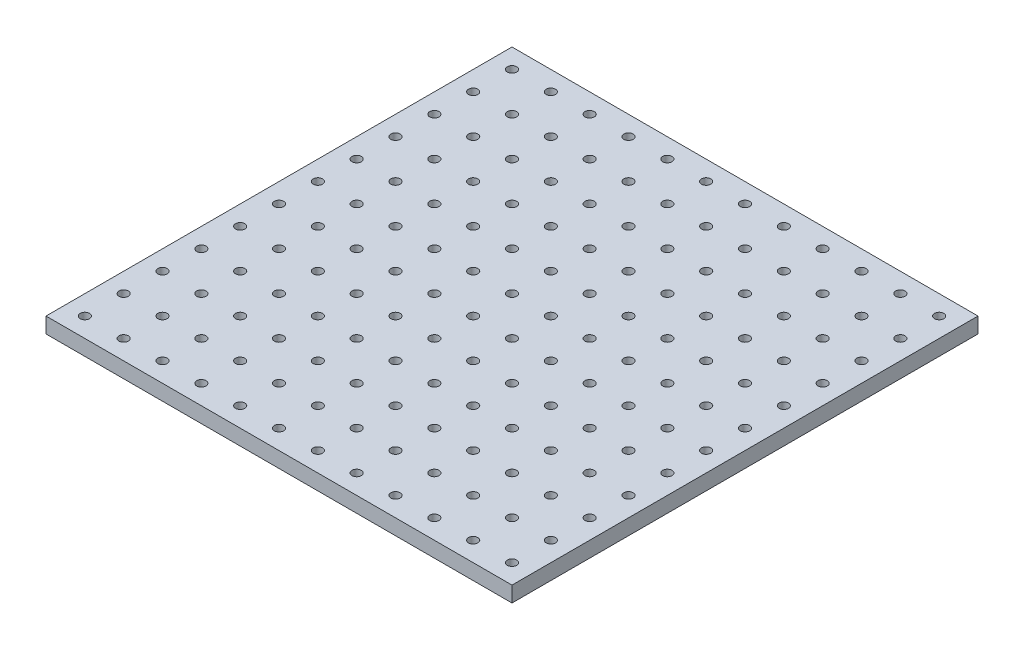
SolidWorks part; units mm, degrees
ref_plane "정면" through (0, 0, 0) normal (0, 0, 1) x (1, 0, 0)
ref_plane "윗면" through (0, 0, 0) normal (0, 1, 0) x (1, 0, 0)
ref_plane "우측면" through (0, 0, 0) normal (1, 0, 0) x (0, 0, -1)
sketch "스케치2" plane through (0, 0, 0) normal (0, 1, 0) x (1, 0, 0)
  line L1 (-150, 150) -> (150, 150)
  line L2 (-150, 150) -> (-150, -150)
  line L3 (-150, -150) -> (150, -150)
  line L4 (150, 150) -> (150, -150)
  circle A0 centre (-137.5, -137.5) radius 3
  circle A1 centre (-112.5, -137.5) radius 3
  circle A2 centre (-87.5, -137.5) radius 3
  circle A3 centre (-62.5, -137.5) radius 3
  circle A4 centre (-37.5, -137.5) radius 3
  circle A5 centre (-12.5, -137.5) radius 3
  circle A6 centre (12.5, -137.5) radius 3
  circle A7 centre (37.5, -137.5) radius 3
  circle A8 centre (62.5, -137.5) radius 3
  circle A9 centre (87.5, -137.5) radius 3
  circle A10 centre (112.5, -137.5) radius 3
  circle A11 centre (137.5, -137.5) radius 3
  circle A12 centre (-112.5, -112.5) radius 3
  circle A13 centre (-87.5, -112.5) radius 3
  circle A14 centre (-62.5, -112.5) radius 3
  circle A15 centre (-37.5, -112.5) radius 3
  circle A16 centre (-12.5, -112.5) radius 3
  circle A17 centre (12.5, -112.5) radius 3
  circle A18 centre (37.5, -112.5) radius 3
  circle A19 centre (62.5, -112.5) radius 3
  circle A20 centre (87.5, -112.5) radius 3
  circle A21 centre (112.5, -112.5) radius 3
  circle A22 centre (137.5, -112.5) radius 3
  circle A23 centre (-112.5, -87.5) radius 3
  circle A24 centre (-87.5, -87.5) radius 3
  circle A25 centre (-62.5, -87.5) radius 3
  circle A26 centre (-37.5, -87.5) radius 3
  circle A27 centre (-12.5, -87.5) radius 3
  circle A28 centre (12.5, -87.5) radius 3
  circle A29 centre (37.5, -87.5) radius 3
  circle A30 centre (62.5, -87.5) radius 3
  circle A31 centre (87.5, -87.5) radius 3
  circle A32 centre (112.5, -87.5) radius 3
  circle A33 centre (137.5, -87.5) radius 3
  circle A34 centre (-112.5, -62.5) radius 3
  circle A35 centre (-87.5, -62.5) radius 3
  circle A36 centre (-62.5, -62.5) radius 3
  circle A37 centre (-37.5, -62.5) radius 3
  circle A38 centre (-12.5, -62.5) radius 3
  circle A39 centre (12.5, -62.5) radius 3
  circle A40 centre (37.5, -62.5) radius 3
  circle A41 centre (62.5, -62.5) radius 3
  circle A42 centre (87.5, -62.5) radius 3
  circle A43 centre (112.5, -62.5) radius 3
  circle A44 centre (137.5, -62.5) radius 3
  circle A45 centre (-112.5, -37.5) radius 3
  circle A46 centre (-87.5, -37.5) radius 3
  circle A47 centre (-62.5, -37.5) radius 3
  circle A48 centre (-37.5, -37.5) radius 3
  circle A49 centre (-12.5, -37.5) radius 3
  circle A50 centre (12.5, -37.5) radius 3
  circle A51 centre (37.5, -37.5) radius 3
  circle A52 centre (62.5, -37.5) radius 3
  circle A53 centre (87.5, -37.5) radius 3
  circle A54 centre (112.5, -37.5) radius 3
  circle A55 centre (137.5, -37.5) radius 3
  circle A56 centre (-112.5, -12.5) radius 3
  circle A57 centre (-87.5, -12.5) radius 3
  circle A58 centre (-62.5, -12.5) radius 3
  circle A59 centre (-37.5, -12.5) radius 3
  circle A60 centre (-12.5, -12.5) radius 3
  circle A61 centre (12.5, -12.5) radius 3
  circle A62 centre (37.5, -12.5) radius 3
  circle A63 centre (62.5, -12.5) radius 3
  circle A64 centre (87.5, -12.5) radius 3
  circle A65 centre (112.5, -12.5) radius 3
  circle A66 centre (137.5, -12.5) radius 3
  circle A67 centre (-112.5, 12.5) radius 3
  circle A68 centre (-87.5, 12.5) radius 3
  circle A69 centre (-62.5, 12.5) radius 3
  circle A70 centre (-37.5, 12.5) radius 3
  circle A71 centre (-12.5, 12.5) radius 3
  circle A72 centre (12.5, 12.5) radius 3
  circle A73 centre (37.5, 12.5) radius 3
  circle A74 centre (62.5, 12.5) radius 3
  circle A75 centre (87.5, 12.5) radius 3
  circle A76 centre (112.5, 12.5) radius 3
  circle A77 centre (137.5, 12.5) radius 3
  circle A78 centre (-112.5, 37.5) radius 3
  circle A79 centre (-87.5, 37.5) radius 3
  circle A80 centre (-62.5, 37.5) radius 3
  circle A81 centre (-37.5, 37.5) radius 3
  circle A82 centre (-12.5, 37.5) radius 3
  circle A83 centre (12.5, 37.5) radius 3
  circle A84 centre (37.5, 37.5) radius 3
  circle A85 centre (62.5, 37.5) radius 3
  circle A86 centre (87.5, 37.5) radius 3
  circle A87 centre (112.5, 37.5) radius 3
  circle A88 centre (137.5, 37.5) radius 3
  circle A89 centre (-112.5, 62.5) radius 3
  circle A90 centre (-87.5, 62.5) radius 3
  circle A91 centre (-62.5, 62.5) radius 3
  circle A92 centre (-37.5, 62.5) radius 3
  circle A93 centre (-12.5, 62.5) radius 3
  circle A94 centre (12.5, 62.5) radius 3
  circle A95 centre (37.5, 62.5) radius 3
  circle A96 centre (62.5, 62.5) radius 3
  circle A97 centre (87.5, 62.5) radius 3
  circle A98 centre (112.5, 62.5) radius 3
  circle A99 centre (137.5, 62.5) radius 3
  circle A100 centre (-112.5, 87.5) radius 3
  circle A101 centre (-87.5, 87.5) radius 3
  circle A102 centre (-62.5, 87.5) radius 3
  circle A103 centre (-37.5, 87.5) radius 3
  circle A104 centre (-12.5, 87.5) radius 3
  circle A105 centre (12.5, 87.5) radius 3
  circle A106 centre (37.5, 87.5) radius 3
  circle A107 centre (62.5, 87.5) radius 3
  circle A108 centre (87.5, 87.5) radius 3
  circle A109 centre (112.5, 87.5) radius 3
  circle A110 centre (137.5, 87.5) radius 3
  circle A111 centre (-112.5, 112.5) radius 3
  circle A112 centre (-87.5, 112.5) radius 3
  circle A113 centre (-62.5, 112.5) radius 3
  circle A114 centre (-37.5, 112.5) radius 3
  circle A115 centre (-12.5, 112.5) radius 3
  circle A116 centre (12.5, 112.5) radius 3
  circle A117 centre (37.5, 112.5) radius 3
  circle A118 centre (62.5, 112.5) radius 3
  circle A119 centre (87.5, 112.5) radius 3
  circle A120 centre (112.5, 112.5) radius 3
  circle A121 centre (137.5, 112.5) radius 3
  circle A122 centre (-112.5, 137.5) radius 3
  circle A123 centre (-87.5, 137.5) radius 3
  circle A124 centre (-62.5, 137.5) radius 3
  circle A125 centre (-37.5, 137.5) radius 3
  circle A126 centre (-12.5, 137.5) radius 3
  circle A127 centre (12.5, 137.5) radius 3
  circle A128 centre (37.5, 137.5) radius 3
  circle A129 centre (62.5, 137.5) radius 3
  circle A130 centre (87.5, 137.5) radius 3
  circle A131 centre (112.5, 137.5) radius 3
  circle A132 centre (137.5, 137.5) radius 3
  circle A133 centre (-137.5, -112.5) radius 3
  circle A134 centre (-137.5, -87.5) radius 3
  circle A135 centre (-137.5, -62.5) radius 3
  circle A136 centre (-137.5, -37.5) radius 3
  circle A137 centre (-137.5, -12.5) radius 3
  circle A138 centre (-137.5, 12.5) radius 3
  circle A139 centre (-137.5, 37.5) radius 3
  circle A140 centre (-137.5, 62.5) radius 3
  circle A141 centre (-137.5, 87.5) radius 3
  circle A142 centre (-137.5, 112.5) radius 3
  circle A143 centre (-137.5, 137.5) radius 3
  point P4 (0, 150)
  point P6 (150, 0)
  dimension "D3" = 6
  dimension "D8" = 25
  dimension "D1" = 300
  dimension "D2" = 300
  dimension "D4" = 12.5
  dimension "D5" = 12.5
  dimension "D9" = 25
  dimension "D6" = 12
  dimension "D7" = 12
extrude "보스-돌출2" add sketch "스케치2" along normal blind 10
